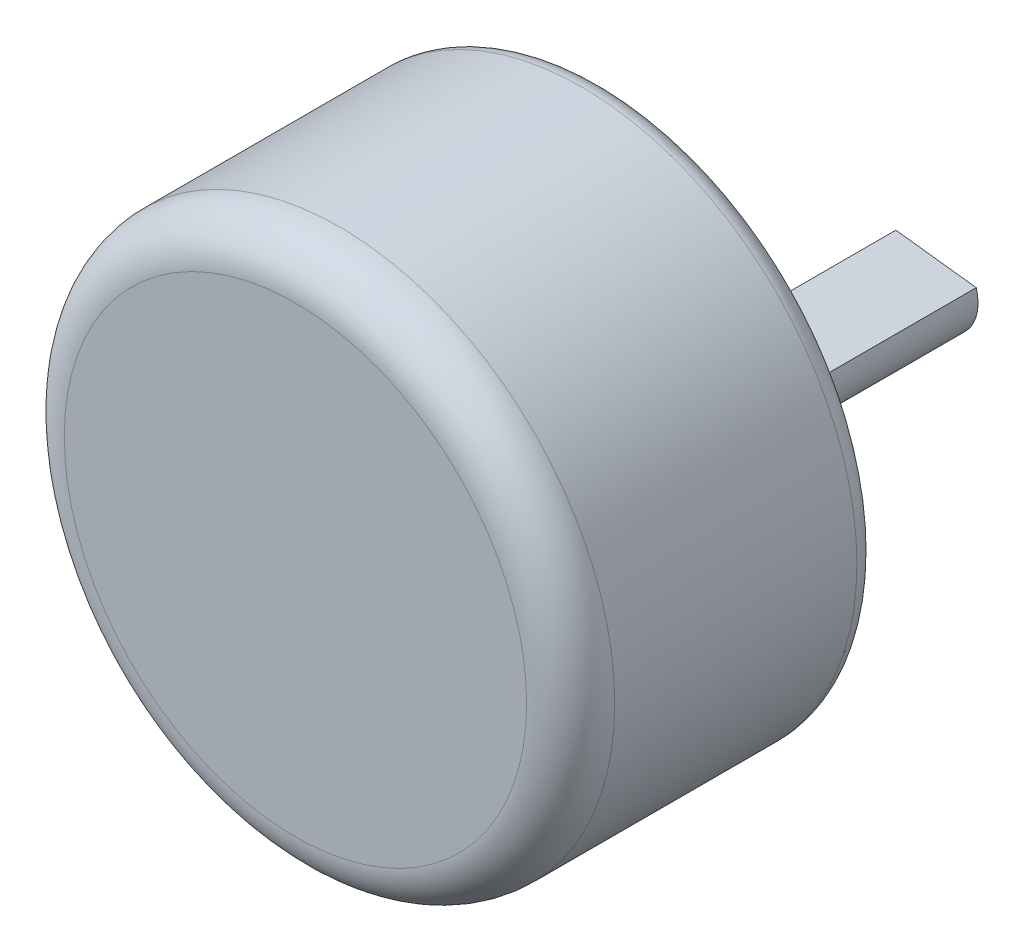
SolidWorks part; units mm, degrees
ref_plane "Front Plane" through (0, 0, 0) normal (0, 0, 1) x (1, 0, 0)
ref_plane "Top Plane" through (0, 0, 0) normal (0, 1, 0) x (1, 0, 0)
ref_plane "Right Plane" through (0, 0, 0) normal (1, 0, 0) x (0, 0, -1)
sketch "Sketch1" plane through (0, 0, 0) normal (0, 0, 1) x (1, 0, 0)
  circle A0 centre (0, 0) radius 12.5
  dimension "D1" = 25
extrude "Boss-Extrude1" add sketch "Sketch1" along normal blind 14
fillet "Fillet2" radius 1 1 edges at (12.5, 0, 0)
sketch "Sketch6" plane through (0, 0, 0) normal (0, 0, -1) x (-1, 0, 0)
  circle A0 centre (-9.5, 0) radius 1
  circle A1 centre (9.5, 0) radius 1
  dimension "D3" = 2
  dimension "D4" = 2
  dimension "D1" = 9.5
  dimension "D2" = 9.5
extrude "Cut-Extrude2" cut sketch "Sketch6" against normal blind 5
sketch "Sketch7" plane through (0, 0, 0) normal (0, 0, -1) x (-1, 0, 0)
  line L0 (0, 0) -> (0, -3) construction
  circle A0 centre (0, -3) radius 4.25
  dimension "D1" = 8.5
  dimension "D2" = 3
extrude "Boss-Extrude5" add sketch "Sketch7" along normal blind 3
fillet "Fillet4" radius 0.5 1 edges at (-4.25, -3, -3)
sketch "Sketch8" plane through (0, 0, -3) normal (0, 0, -1) x (-1, 0, 0)
  circle A0 centre (0, -3) radius 2
extrude "Boss-Extrude6" add sketch "Sketch8" along normal blind 12
sketch "Sketch9" plane through (0, 0, -15) normal (0, 0, -1) x (-1, 0, 0)
  line L0 (-1.9191, -2.4368) -> (1.732, -1.9998)
  circle A0 centre (0, -3) radius 2 construction
extrude "Cut-Extrude3" cut sketch "Sketch9" against normal blind 9 and the other way through all
fillet "Fillet5" radius 2 1 edges at (12.5, 0, 14)
